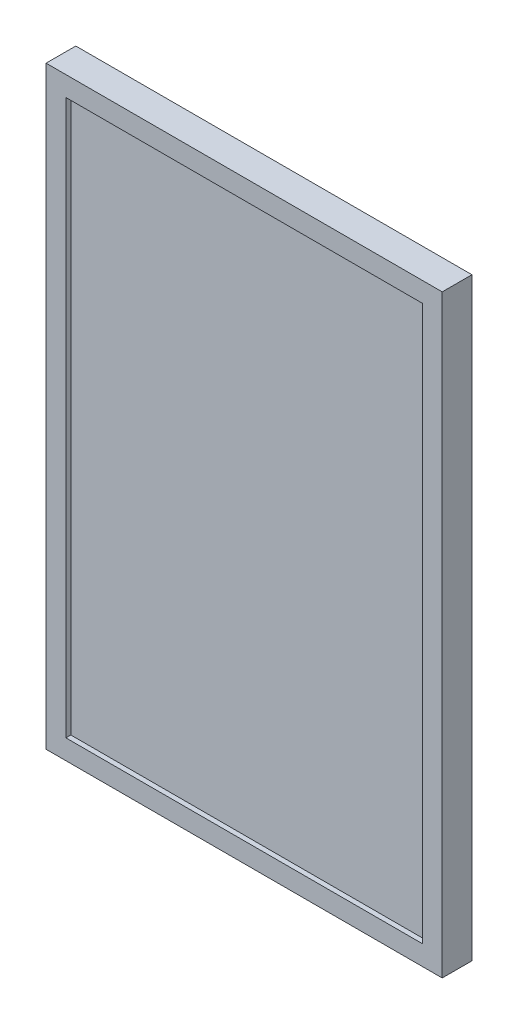
SolidWorks part; units mm, degrees
ref_plane "Front Plane" through (0, 0, 0) normal (0, 0, 1) x (1, 0, 0)
ref_plane "Top Plane" through (0, 0, 0) normal (0, 1, 0) x (1, 0, 0)
ref_plane "Right Plane" through (0, 0, 0) normal (1, 0, 0) x (0, 0, -1)
sketch "Sketch4" plane through (0, 0, 0) normal (0, 0, 1) x (1, 0, 0)
  line L1 (-50.2324, 57.0436) -> (51.3676, 57.0436)
  line L2 (-50.2324, 57.0436) -> (-50.2324, -95.3564)
  line L3 (-50.2324, -95.3564) -> (51.3676, -95.3564)
  line L4 (51.3676, 57.0436) -> (51.3676, -95.3564)
  dimension "D1" = 101.6
  dimension "D2" = 152.4
extrude "Boss-Extrude3" add sketch "Sketch4" along normal blind 7.62
sketch "Sketch5" plane through (0, 0, 7.62) normal (0, 0, 1) x (1, 0, 0)
  line L0 (51.3676, -95.3564) -> (51.3676, 57.0436) construction
  line L1 (-45.1524, 51.9636) -> (46.2876, 51.9636)
  line L2 (-45.1524, 51.9636) -> (-45.1524, -90.2764)
  line L3 (-45.1524, -90.2764) -> (46.2876, -90.2764)
  line L4 (46.2876, 51.9636) -> (46.2876, -90.2764)
  line L5 (-50.2324, 57.0436) -> (-50.2324, -95.3564) construction
  line L6 (51.3676, 57.0436) -> (-50.2324, 57.0436) construction
  line L7 (-50.2324, -95.3564) -> (51.3676, -95.3564) construction
  point P6 (0, 0)
  point P9 (0, 0)
  point P12 (0, 0)
  point P15 (0, 0)
  point P16 (-45.1524, 51.9636)
  point P17 (-45.1524, 51.9636)
  dimension "D1" = 5.08
  dimension "D2" = 5.08
  dimension "D3" = 5.08
  dimension "D4" = 5.08
  dimension "D5" = 91.44
  dimension "D6" = 142.24
extrude "Cut-Extrude1" cut sketch "Sketch5" against normal blind 1.27 contours L1 L4 L3 L2
sketch "Sketch10" plane through (0, 0, 6.35) normal (0, 0, 1) x (1, 0, 0)
  line L0 (0.5676, 51.9636) -> (-11.3643, 18.4652)
  line L1 (-45.1524, 51.9636) -> (46.2876, 51.9636) construction
  line L2 (-11.3643, 18.4652) -> (-3.6021, 18.4652)
  line L3 (-3.6021, 18.4652) -> (-3.6021, -7.9584)
  line L4 (-3.6021, -7.9584) -> (-11.1342, -7.9584)
  line L5 (-11.1342, -7.9584) -> (-21.091, 9.2065)
  line L6 (-21.091, 9.2065) -> (-19.0155, 15.0334)
  line L7 (-19.0155, 15.0334) -> (-39.1339, 24.6187)
  line L8 (-39.1339, 24.6187) -> (-14.8993, -17.1602)
  line L9 (-14.8993, -17.1602) -> (-4.2904, -17.1602)
  line L10 (-4.2904, -17.1602) -> (-4.2904, -90.2764)
  line L11 (0.5676, 51.9636) -> (15.1416, 18.4652)
  line L12 (15.1416, 18.4652) -> (6.6681, 18.4652)
  line L13 (6.6681, 18.4652) -> (6.6681, -7.5927)
  line L14 (6.6681, -7.5927) -> (14.2881, -7.5927)
  line L15 (14.2881, -7.5927) -> (24.328, 9.5723)
  line L16 (24.328, 9.5723) -> (22.0352, 13.7299)
  line L17 (22.0352, 13.7299) -> (41.2589, 24.3311)
  line L18 (41.2589, 24.3311) -> (18.5686, -17.6355)
  line L19 (18.5686, -17.6355) -> (7.3688, -17.6355)
  line L20 (7.3688, -17.6355) -> (7.3688, -90.2764)
  line L21 (-45.1524, -90.2764) -> (46.2876, -90.2764) construction
  line L22 (-45.1524, -90.2764) -> (46.2876, -90.2764) construction
  line L23 (-4.2904, -90.2764) -> (7.3688, -90.2764)
  point P4 (25.1815, 9.073)
  point P24 (0, 0)
  point P25 (40.7272, 24.6187)
  point P26 (0, 0)
